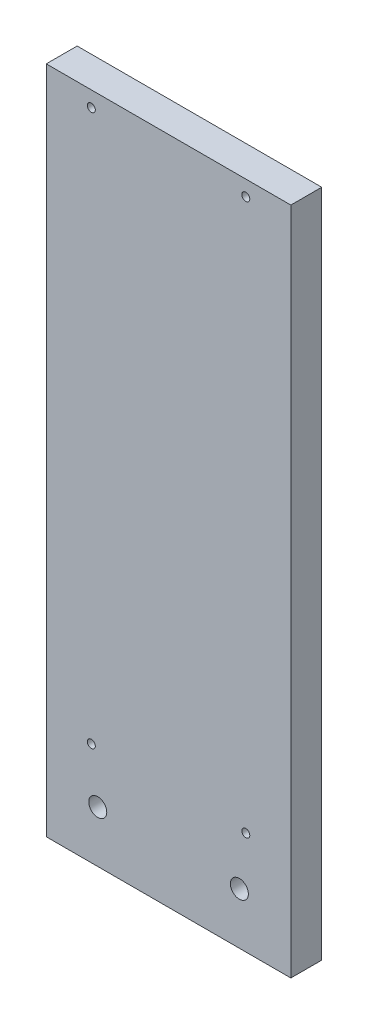
SolidWorks part; units mm, degrees
ref_plane "Front Plane" through (0, 0, 0) normal (0, 0, 1) x (1, 0, 0)
ref_plane "Top Plane" through (0, 0, 0) normal (0, 1, 0) x (1, 0, 0)
ref_plane "Right Plane" through (0, 0, 0) normal (1, 0, 0) x (0, 0, -1)
sketch "Sketch1" plane through (0, 0, 0) normal (0, 0, 1) x (1, 0, 0)
  line L1 (-47.5, 130) -> (47.5, 130)
  line L2 (-47.5, 130) -> (-47.5, -130)
  line L3 (-47.5, -130) -> (47.5, -130)
  line L4 (47.5, 130) -> (47.5, -130)
  line L5 (-47.5, 130) -> (47.5, -130) construction
  line L6 (-47.5, -130) -> (47.5, 130) construction
  point P0 (0, 0)
  dimension "D1" = 95
  dimension "D2" = 260
extrude "Boss-Extrude1" add sketch "Sketch1" along normal blind 12
sketch "Sketch3" plane through (0, 0, 12) normal (0, 0, 1) x (1, 0, 0)
  line L0 (-47.5, 130) -> (-47.5, -130) construction
  line L1 (47.5, -130) -> (47.5, 130) construction
  line L2 (-47.5, -130) -> (47.5, -130) construction
  circle A0 centre (-27.5, -110) radius 3.5
  circle A1 centre (27.5, -110) radius 3.5
  dimension "D1" = 7
  dimension "D2" = 7
  dimension "D3" = 20
  dimension "D4" = 20
  dimension "D5" = 20
  dimension "D6" = 20
extrude "Cut-Extrude1" cut sketch "Sketch3" against normal through all
sketch "Sketch4" plane through (0, 0, 12) normal (0, 0, 1) x (1, 0, 0)
  line L0 (-47.5, -130) -> (47.5, -130) construction
  line L1 (-47.5, 130) -> (-47.5, -130) construction
  line L2 (47.5, -130) -> (47.5, 130) construction
  line L3 (47.5, -130) -> (47.5, 130) construction
  line L4 (-47.5, 130) -> (-47.5, -130) construction
  line L5 (47.5, 130) -> (-47.5, 130) construction
  circle A0 centre (-30, -90) radius 1.55
  circle A1 centre (30, -90) radius 1.55
  circle A2 centre (30, 124) radius 1.55
  circle A3 centre (-30, 124) radius 1.55
  dimension "D1" = 3.1
  dimension "D2" = 3.1
  dimension "D7" = 3.1
  dimension "D8" = 3.1
  dimension "D3" = 40
  dimension "D4" = 40
  dimension "D5" = 17.5
  dimension "D6" = 17.5
  dimension "D9" = 17.5
  dimension "D10" = 17.5
  dimension "D11" = 6
  dimension "D12" = 6
extrude "Cut-Extrude2" cut sketch "Sketch4" against normal through all
